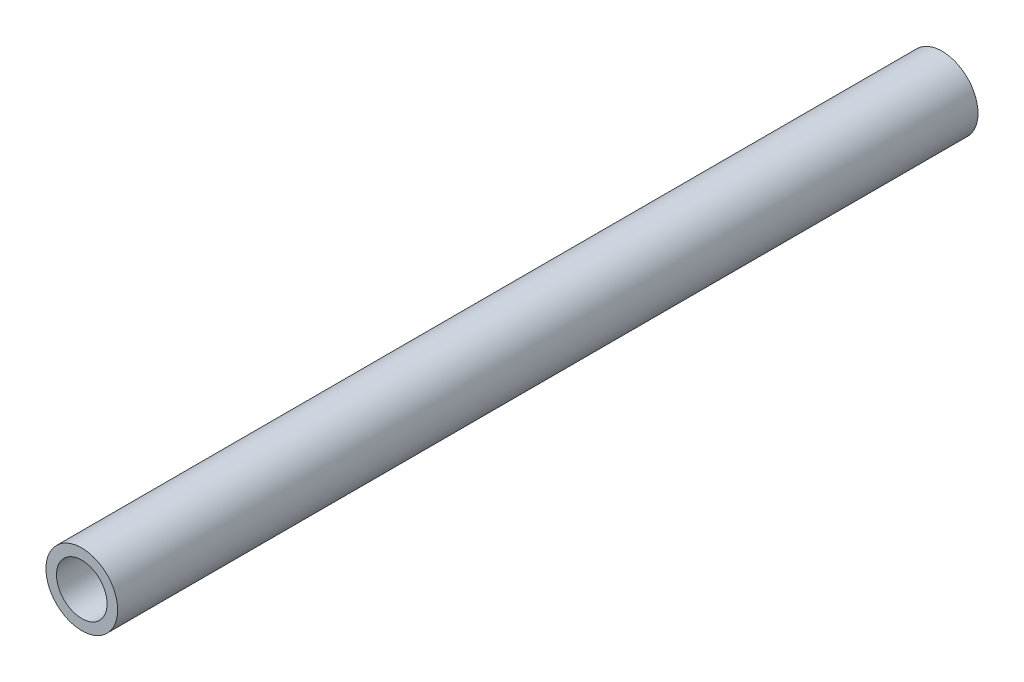
SolidWorks part; units mm, degrees
material "PVC Rigid"
ref_plane "Front Plane" through (0, 0, 0) normal (0, 0, 1) x (1, 0, 0)
ref_plane "Top Plane" through (0, 0, 0) normal (0, 1, 0) x (1, 0, 0)
ref_plane "Right Plane" through (0, 0, 0) normal (1, 0, 0) x (0, 0, -1)
sketch "Sketch2" plane through (0, 0, 0) normal (0, 0, 1) x (1, 0, 0)
  circle A0 centre (0, 0) radius 6.35
  circle A2 centre (0, 0) radius 4.4831
  dimension "D1" = 12.7
  dimension "D2" = 1.8669
extrude "Boss-Extrude1" add sketch "Sketch2" along normal blind 152.4
